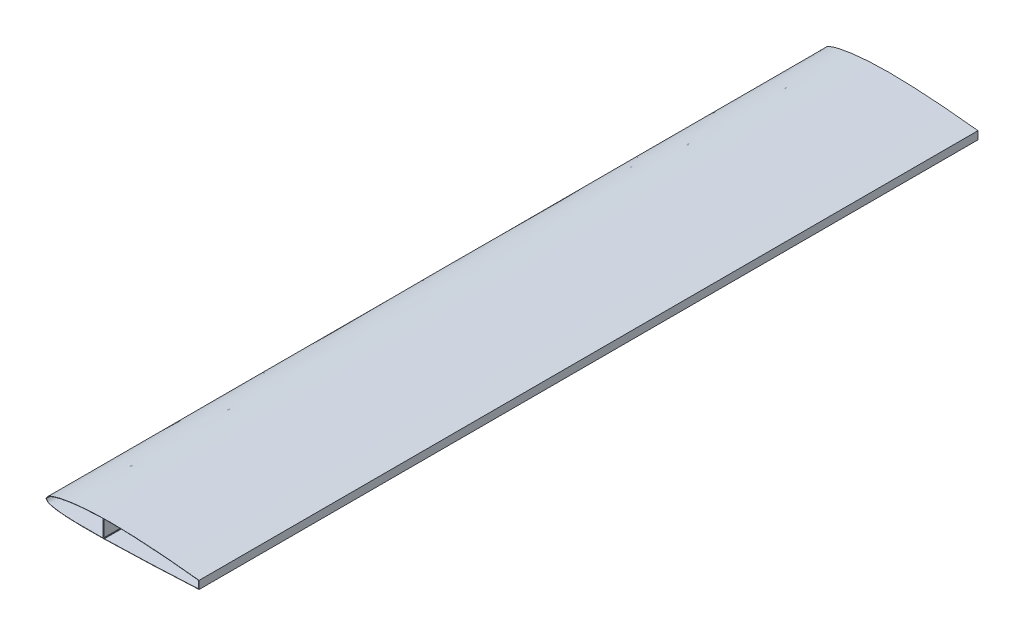
SolidWorks part; units mm, degrees
material "2024-T4"
ref_plane "Front Plane" through (0, 0, 0) normal (0, 0, 1) x (1, 0, 0)
ref_plane "Top Plane" through (0, 0, 0) normal (0, 1, 0) x (1, 0, 0)
ref_plane "Right Plane" through (0, 0, 0) normal (1, 0, 0) x (0, 0, -1)
curve "Top"
  spline degree 3 poles (0, 0, 0) (3.9101, 6.7289, 0) (10.5058, 18.0795, 0) (27.0112, 25.6481, 0) (40.59, 31.5719, 0) (54.3011, 36.3192, 0) (67.915, 40.4922, 0) (81.5319, 44.1857, 0) (95.1379, 47.5159, 0) (108.7414, 50.5421, 0) (122.3424, 53.3102, 0) (135.9422, 55.8531, 0) (149.541, 58.1958, 0) (163.1392, 60.3581, 0) (176.737, 62.3558, 0) (190.3344, 64.202, 0) (203.9316, 65.9075, 0) (217.5286, 67.4816, 0) (231.1254, 68.9321, 0) (244.7221, 70.2661, 0) (258.3187, 71.4894, 0) (271.9153, 72.6074, 0) (285.5117, 73.625, 0) (299.1081, 74.5462, 0) (312.7045, 75.3751, 0) (326.3008, 76.1151, 0) (339.8971, 76.7695, 0) (353.4934, 77.341, 0) (367.0896, 77.8326, 0) (380.6858, 78.2467, 0) (394.282, 78.5855, 0) (407.8782, 78.8514, 0) (421.4743, 79.0463, 0) (435.0705, 79.172, 0) (448.6666, 79.2305, 0) (462.2627, 79.2233, 0) (475.8588, 79.1521, 0) (489.4549, 79.0183, 0) (503.051, 78.8233, 0) (516.6471, 78.5684, 0) (530.2431, 78.2555, 0) (543.839, 77.8832, 0) (557.435, 77.469, 0) (571.031, 77.0139, 0) (584.627, 76.5188, 0) (598.223, 75.9847, 0) (611.819, 75.4126, 0) (625.415, 74.8034, 0) (639.011, 74.1578, 0) (652.607, 73.4767, 0) (666.2029, 72.761, 0) (679.7989, 72.0111, 0) (693.3949, 71.228, 0) (706.9909, 70.4122, 0) (720.5869, 69.5644, 0) (734.1828, 68.6851, 0) (747.7788, 67.7749, 0) (761.3748, 66.8344, 0) (774.9708, 65.864, 0) (788.5667, 64.8643, 0) (802.1627, 63.8356, 0) (815.7587, 62.7784, 0) (829.3546, 61.6931, 0) (842.9506, 60.58, 0) (856.5466, 59.4396, 0) (870.1426, 58.2721, 0) (883.7385, 57.0778, 0) (897.3345, 55.8569, 0) (910.9305, 54.6099, 0) (924.5265, 53.3368, 0) (938.1224, 52.0379, 0) (951.7184, 50.7134, 0) (965.3144, 49.3633, 0) (978.9104, 47.988, 0) (992.5063, 46.5875, 0) (1006.1023, 45.1619, 0) (1019.6983, 43.7112, 0) (1033.2943, 42.2356, 0) (1046.8903, 40.7351, 0) (1060.4862, 39.2096, 0) (1074.0822, 37.6593, 0) (1087.6782, 36.0841, 0) (1101.2742, 34.4839, 0) (1114.8702, 32.8588, 0) (1128.4662, 31.2085, 0) (1142.0622, 29.5331, 0) (1155.6581, 27.8325, 0) (1169.2541, 26.1064, 0) (1182.8501, 24.3548, 0) (1196.4461, 22.5774, 0) (1210.0421, 20.7742, 0) (1223.6381, 18.9448, 0) (1237.2341, 17.0892, 0) (1250.8301, 15.207, 0) (1264.4261, 13.2979, 0) (1278.0221, 11.3619, 0) (1291.6181, 9.3984, 0) (1305.2142, 7.4073, 0) (1318.8101, 5.3878, 0) (1332.4064, 3.3419, 0) (1341.4683, 1.954, 0) (1346, 1.26, 0) knots 0 0 0 0 0.016572 0.027954 0.03876 0.049312 0.059718 0.070028 0.080271 0.090463 0.100615 0.110735 0.12083 0.130902 0.140957 0.150996 0.161021 0.171035 0.181039 0.191035 0.201022 0.211003 0.220979 0.230949 0.240915 0.250877 0.260836 0.270792 0.280746 0.290699 0.300649 0.310598 0.320547 0.330495 0.340442 0.35039 0.360338 0.370286 0.380234 0.390183 0.400133 0.410084 0.420037 0.42999 0.439944 0.449899 0.459855 0.469813 0.479771 0.489731 0.499692 0.509655 0.519619 0.529584 0.539551 0.549519 0.559489 0.56946 0.579433 0.589407 0.599383 0.609361 0.61934 0.629321 0.639303 0.649287 0.659273 0.66926 0.67925 0.689241 0.699233 0.709228 0.719224 0.729223 0.739223 0.749225 0.759229 0.769235 0.779242 0.789252 0.799264 0.809278 0.819294 0.829313 0.839333 0.849356 0.859381 0.869408 0.879438 0.88947 0.899505 0.909542 0.919581 0.929624 0.939669 0.949717 0.959767 0.969821 0.979878 0.989937 1 1 1 1
curve "Bot"
  spline degree 3 poles (0, 0, 0) (3.9391, -6.157, 0) (10.6258, -16.6087, 0) (27.1033, -21.7439, 0) (40.6414, -25.7752, 0) (54.341, -28.6555, 0) (67.9447, -31.0337, 0) (81.556, -32.9828, 0) (95.1576, -34.6222, 0) (108.758, -36.0091, 0) (122.3566, -37.1896, 0) (135.9545, -38.1961, 0) (149.5518, -39.0537, 0) (163.1487, -39.782, 0) (176.7454, -40.3968, 0) (190.3419, -40.9112, 0) (203.9383, -41.3361, 0) (217.5345, -41.6805, 0) (231.1307, -41.9525, 0) (244.7269, -42.1589, 0) (258.323, -42.3057, 0) (271.9191, -42.3982, 0) (285.5151, -42.4413, 0) (299.1111, -42.4392, 0) (312.7072, -42.3956, 0) (326.3032, -42.3143, 0) (339.8991, -42.1982, 0) (353.4951, -42.0505, 0) (367.0911, -41.8737, 0) (380.6871, -41.6705, 0) (394.283, -41.4431, 0) (407.879, -41.1937, 0) (421.4749, -40.9243, 0) (435.0709, -40.6368, 0) (448.6668, -40.3331, 0) (462.2628, -40.0147, 0) (475.8587, -39.6833, 0) (489.4547, -39.3403, 0) (503.0506, -38.9872, 0) (516.6466, -38.6254, 0) (530.2425, -38.2555, 0) (543.8386, -37.8813, 0) (557.4346, -37.4875, 0) (571.0306, -37.0754, 0) (584.6265, -36.6461, 0) (598.2225, -36.2004, 0) (611.8184, -35.7394, 0) (625.4144, -35.264, 0) (639.0103, -34.7749, 0) (652.6063, -34.2729, 0) (666.2022, -33.7589, 0) (679.7982, -33.2336, 0) (693.3941, -32.6976, 0) (706.9901, -32.1516, 0) (720.586, -31.5963, 0) (734.182, -31.0322, 0) (747.7779, -30.4598, 0) (761.3739, -29.8798, 0) (774.9698, -29.2926, 0) (788.5658, -28.6987, 0) (802.1617, -28.0986, 0) (815.7577, -27.4926, 0) (829.3536, -26.8812, 0) (842.9496, -26.2647, 0) (856.5456, -25.6434, 0) (870.1415, -25.0178, 0) (883.7375, -24.3881, 0) (897.3334, -23.7545, 0) (910.9294, -23.1174, 0) (924.5253, -22.4769, 0) (938.1213, -21.8332, 0) (951.7172, -21.1866, 0) (965.3132, -20.5372, 0) (978.9092, -19.8852, 0) (992.5051, -19.2306, 0) (1006.1011, -18.5736, 0) (1019.697, -17.9143, 0) (1033.293, -17.2526, 0) (1046.8889, -16.5888, 0) (1060.4849, -15.9227, 0) (1074.0809, -15.2544, 0) (1087.6768, -14.5838, 0) (1101.2728, -13.911, 0) (1114.8687, -13.2359, 0) (1128.4647, -12.5583, 0) (1142.0607, -11.8783, 0) (1155.6566, -11.1957, 0) (1169.2526, -10.5103, 0) (1182.8486, -9.8221, 0) (1196.4445, -9.1308, 0) (1210.0405, -8.4363, 0) (1223.6365, -7.7383, 0) (1237.2324, -7.0368, 0) (1250.8284, -6.3313, 0) (1264.4244, -5.6217, 0) (1278.0203, -4.9077, 0) (1291.6163, -4.1891, 0) (1305.2123, -3.4654, 0) (1318.8082, -2.7363, 0) (1332.4042, -2.002, 0) (1341.468, -1.5073, 0) (1346, -1.26, 0) knots 0 0 0 0 0.01554 0.02638 0.036798 0.047053 0.057224 0.067347 0.077439 0.08751 0.097567 0.107613 0.117652 0.127685 0.137714 0.14774 0.157763 0.167785 0.177806 0.187826 0.197845 0.207864 0.217882 0.227901 0.23792 0.247939 0.257958 0.267977 0.277996 0.288016 0.298036 0.308056 0.318077 0.328098 0.338119 0.34814 0.358162 0.368184 0.378206 0.388228 0.39825 0.408273 0.418296 0.428319 0.438343 0.448367 0.458391 0.468416 0.478441 0.488466 0.498492 0.508518 0.518545 0.528571 0.538598 0.548626 0.558653 0.568681 0.578709 0.588737 0.598765 0.608794 0.618823 0.628852 0.638881 0.64891 0.658939 0.668969 0.678999 0.689028 0.699058 0.709088 0.719118 0.729148 0.739179 0.749209 0.759239 0.76927 0.7793 0.789331 0.799362 0.809393 0.819424 0.829455 0.839486 0.849517 0.859548 0.869579 0.879611 0.889642 0.899674 0.909706 0.919738 0.92977 0.939802 0.949835 0.959867 0.9699 0.979933 0.989967 1 1 1 1
sketch "Sketch3" plane through (0, 0, 0) normal (0, 0, 1) x (1, 0, 0)
  line L1 (0, 0) -> (1076.8, 0) construction
  line L2 (1076.8, 37.3423) -> (1076.8, -15.1201)
  line L3 (1078.8, 39.1249) -> (1078.8, -17.024)
  line L4 (1077.8, 38.2336) -> (1077.8, -16.072) construction
  spline S0 degree 3 poles (-1345.7363, -1475.2093) (73.9863, 287.8593) (-51.0903, 2.6251) (27.1033, -21.7439) (40.6414, -25.7752) (54.341, -28.6555) (67.9447, -31.0337) (81.556, -32.9828) (95.1576, -34.6222) (108.758, -36.0091) (122.3566, -37.1896) (135.9545, -38.1961) (149.5518, -39.0537) (163.1487, -39.782) (176.7454, -40.3968) (190.3419, -40.9112) (203.9383, -41.3361) (217.5345, -41.6805) (231.1307, -41.9525) (244.7269, -42.1589) (258.323, -42.3057) (271.9191, -42.3982) (285.5151, -42.4413) (299.1111, -42.4392) (312.7072, -42.3956) (326.3032, -42.3143) (339.8991, -42.1982) (353.4951, -42.0505) (367.0911, -41.8737) (380.6871, -41.6705) (394.283, -41.4431) (407.879, -41.1937) (421.4749, -40.9243) (435.0709, -40.6368) (448.6668, -40.3331) (462.2628, -40.0147) (475.8587, -39.6833) (489.4547, -39.3403) (503.0506, -38.9872) (516.6466, -38.6254) (530.2425, -38.2555) (543.8386, -37.8813) (557.4346, -37.4875) (571.0306, -37.0754) (584.6265, -36.6461) (598.2225, -36.2004) (611.8184, -35.7394) (625.4144, -35.264) (639.0103, -34.7749) (652.6063, -34.2729) (666.2022, -33.7589) (679.7982, -33.2336) (693.3941, -32.6976) (706.9901, -32.1516) (720.586, -31.5963) (734.182, -31.0322) (747.7779, -30.4598) (761.3739, -29.8798) (774.9698, -29.2926) (788.5658, -28.6987) (802.1617, -28.0986) (815.7577, -27.4926) (829.3536, -26.8812) (842.9496, -26.2647) (856.5456, -25.6434) (870.1415, -25.0178) (883.7375, -24.3881) (897.3334, -23.7545) (910.9294, -23.1174) (924.5253, -22.4769) (938.1213, -21.8332) (951.7172, -21.1866) (965.3132, -20.5372) (978.9092, -19.8852) (992.5051, -19.2306) (1006.1011, -18.5736) (1019.697, -17.9143) (1033.293, -17.2526) (1046.8889, -16.5888) (1060.4849, -15.9227) (1074.0809, -15.2544) (1087.6768, -14.5838) (1101.2728, -13.911) (1114.8687, -13.2359) (1128.4647, -12.5583) (1142.0607, -11.8783) (1155.6566, -11.1957) (1169.2526, -10.5103) (1182.8486, -9.8221) (1196.4445, -9.1308) (1210.0405, -8.4363) (1223.6365, -7.7383) (1237.2324, -7.0368) (1250.8284, -6.3313) (1264.4244, -5.6217) (1278.0203, -4.9077) (1291.6163, -4.1891) (1305.2123, -3.4654) (1318.8082, -2.7363) (1786.1325, 22.5031) (2248.1969, 60.8937) (2777.2036, -1216.076) knots -0.137826 -0.137826 -0.137826 -0.137826 0.01554 0.02638 0.036798 0.047053 0.057224 0.067347 0.077439 0.08751 0.097567 0.107613 0.117652 0.127685 0.137714 0.14774 0.157763 0.167785 0.177806 0.187826 0.197845 0.207864 0.217882 0.227901 0.23792 0.247939 0.257958 0.267977 0.277996 0.288016 0.298036 0.308056 0.318077 0.328098 0.338119 0.34814 0.358162 0.368184 0.378206 0.388228 0.39825 0.408273 0.418296 0.428319 0.438343 0.448367 0.458391 0.468416 0.478441 0.488466 0.498492 0.508518 0.518545 0.528571 0.538598 0.548626 0.558653 0.568681 0.578709 0.588737 0.598765 0.608794 0.618823 0.628852 0.638881 0.64891 0.658939 0.668969 0.678999 0.689028 0.699058 0.709088 0.719118 0.729148 0.739179 0.749209 0.759239 0.76927 0.7793 0.789331 0.799362 0.809393 0.819424 0.829455 0.839486 0.849517 0.859548 0.869579 0.879611 0.889642 0.899674 0.909706 0.919738 0.92977 0.939802 0.949835 0.959867 0.9699 0.979933 0.989967 2.004497 2.004497 2.004497 2.004497 only from (0, 0) to (1346, -1.26) construction
  spline S1 degree 3 poles (-1478.3902, 1341.2037) (85.3471, -283.5176) (-53.2012, -11.1336) (27.0112, 25.6481) (40.59, 31.5719) (54.3011, 36.3192) (67.915, 40.4922) (81.5319, 44.1857) (95.1379, 47.5159) (108.7414, 50.5421) (122.3424, 53.3102) (135.9422, 55.8531) (149.541, 58.1958) (163.1392, 60.3581) (176.737, 62.3558) (190.3344, 64.202) (203.9316, 65.9075) (217.5286, 67.4816) (231.1254, 68.9321) (244.7221, 70.2661) (258.3187, 71.4894) (271.9153, 72.6074) (285.5117, 73.625) (299.1081, 74.5462) (312.7045, 75.3751) (326.3008, 76.1151) (339.8971, 76.7695) (353.4934, 77.341) (367.0896, 77.8326) (380.6858, 78.2467) (394.282, 78.5855) (407.8782, 78.8514) (421.4743, 79.0463) (435.0705, 79.172) (448.6666, 79.2305) (462.2627, 79.2233) (475.8588, 79.1521) (489.4549, 79.0183) (503.051, 78.8233) (516.6471, 78.5684) (530.2431, 78.2555) (543.839, 77.8832) (557.435, 77.469) (571.031, 77.0139) (584.627, 76.5188) (598.223, 75.9847) (611.819, 75.4126) (625.415, 74.8034) (639.011, 74.1578) (652.607, 73.4767) (666.2029, 72.761) (679.7989, 72.0111) (693.3949, 71.228) (706.9909, 70.4122) (720.5869, 69.5644) (734.1828, 68.6851) (747.7788, 67.7749) (761.3748, 66.8344) (774.9708, 65.864) (788.5667, 64.8643) (802.1627, 63.8356) (815.7587, 62.7784) (829.3546, 61.6931) (842.9506, 60.58) (856.5466, 59.4396) (870.1426, 58.2721) (883.7385, 57.0778) (897.3345, 55.8569) (910.9305, 54.6099) (924.5265, 53.3368) (938.1224, 52.0379) (951.7184, 50.7134) (965.3144, 49.3633) (978.9104, 47.988) (992.5063, 46.5875) (1006.1023, 45.1619) (1019.6983, 43.7112) (1033.2943, 42.2356) (1046.8903, 40.7351) (1060.4862, 39.2096) (1074.0822, 37.6593) (1087.6782, 36.0841) (1101.2742, 34.4839) (1114.8702, 32.8588) (1128.4662, 31.2085) (1142.0622, 29.5331) (1155.6581, 27.8325) (1169.2541, 26.1064) (1182.8501, 24.3548) (1196.4461, 22.5774) (1210.0421, 20.7742) (1223.6381, 18.9448) (1237.2341, 17.0892) (1250.8301, 15.207) (1264.4261, 13.2979) (1278.0221, 11.3619) (1291.6181, 9.3984) (1305.2142, 7.4073) (1318.8101, 5.3878) (1630.3994, -41.4976) (1933.3109, -114.9683) (2496.3588, 1552.4265) knots -0.149606 -0.149606 -0.149606 -0.149606 0.016572 0.027954 0.03876 0.049312 0.059718 0.070028 0.080271 0.090463 0.100615 0.110735 0.12083 0.130902 0.140957 0.150996 0.161021 0.171035 0.181039 0.191035 0.201022 0.211003 0.220979 0.230949 0.240915 0.250877 0.260836 0.270792 0.280746 0.290699 0.300649 0.310598 0.320547 0.330495 0.340442 0.35039 0.360338 0.370286 0.380234 0.390183 0.400133 0.410084 0.420037 0.42999 0.439944 0.449899 0.459855 0.469813 0.479771 0.489731 0.499692 0.509655 0.519619 0.529584 0.539551 0.549519 0.559489 0.56946 0.579433 0.589407 0.599383 0.609361 0.61934 0.629321 0.639303 0.649287 0.659273 0.66926 0.67925 0.689241 0.699233 0.709228 0.719224 0.729223 0.739223 0.749225 0.759229 0.769235 0.779242 0.789252 0.799264 0.809278 0.819294 0.829313 0.839333 0.849356 0.859381 0.869408 0.879438 0.88947 0.899505 0.909542 0.919581 0.929624 0.939669 0.949717 0.959767 0.969821 0.979878 0.989937 1.661442 1.661442 1.661442 1.661442 only from (0, 0) to (1346, 1.26) construction
  spline S2 degree 3 poles (0, 0) (3.9391, -6.157) (10.6258, -16.6087) (27.1033, -21.7439) (40.6414, -25.7752) (54.341, -28.6555) (67.9447, -31.0337) (81.556, -32.9828) (95.1576, -34.6222) (108.758, -36.0091) (122.3566, -37.1896) (135.9545, -38.1961) (149.5518, -39.0537) (163.1487, -39.782) (176.7454, -40.3968) (190.3419, -40.9112) (203.9383, -41.3361) (217.5345, -41.6805) (231.1307, -41.9525) (244.7269, -42.1589) (258.323, -42.3057) (271.9191, -42.3982) (285.5151, -42.4413) (299.1111, -42.4392) (312.7072, -42.3956) (326.3032, -42.3143) (339.8991, -42.1982) (353.4951, -42.0505) (367.0911, -41.8737) (380.6871, -41.6705) (394.283, -41.4431) (407.879, -41.1937) (421.4749, -40.9243) (435.0709, -40.6368) (448.6668, -40.3331) (462.2628, -40.0147) (475.8587, -39.6833) (489.4547, -39.3403) (503.0506, -38.9872) (516.6466, -38.6254) (530.2425, -38.2555) (543.8386, -37.8813) (557.4346, -37.4875) (571.0306, -37.0754) (584.6265, -36.6461) (598.2225, -36.2004) (611.8184, -35.7394) (625.4144, -35.264) (639.0103, -34.7749) (652.6063, -34.2729) (666.2022, -33.7589) (679.7982, -33.2336) (693.3941, -32.6976) (706.9901, -32.1516) (720.586, -31.5963) (734.182, -31.0322) (747.7779, -30.4598) (761.3739, -29.8798) (774.9698, -29.2926) (788.5658, -28.6987) (802.1617, -28.0986) (815.7577, -27.4926) (829.3536, -26.8812) (842.9496, -26.2647) (856.5456, -25.6434) (870.1415, -25.0178) (883.7375, -24.3881) (897.3334, -23.7545) (910.9294, -23.1174) (924.5253, -22.4769) (938.1213, -21.8332) (951.7172, -21.1866) (965.3132, -20.5372) (978.9092, -19.8852) (992.5051, -19.2306) (1006.1011, -18.5736) (1019.697, -17.9143) (1033.293, -17.2526) (1046.8889, -16.5888) (1060.4849, -15.9227) (1070.4552, -15.4326) (1075.8936, -15.1647) (1076.8, -15.1201) knots 0 0 0 0 0.01554 0.02638 0.036798 0.047053 0.057224 0.067347 0.077439 0.08751 0.097567 0.107613 0.117652 0.127685 0.137714 0.14774 0.157763 0.167785 0.177806 0.187826 0.197845 0.207864 0.217882 0.227901 0.23792 0.247939 0.257958 0.267977 0.277996 0.288016 0.298036 0.308056 0.318077 0.328098 0.338119 0.34814 0.358162 0.368184 0.378206 0.388228 0.39825 0.408273 0.418296 0.428319 0.438343 0.448367 0.458391 0.468416 0.478441 0.488466 0.498492 0.508518 0.518545 0.528571 0.538598 0.548626 0.558653 0.568681 0.578709 0.588737 0.598765 0.608794 0.618823 0.628852 0.638881 0.64891 0.658939 0.668969 0.678999 0.689028 0.699058 0.709088 0.719118 0.729148 0.739179 0.749209 0.759239 0.76927 0.7793 0.789331 0.799362 0.801368 0.801368 0.801368 0.801368
  spline S3 degree 3 poles (0, 0) (3.9101, 6.7289) (10.5058, 18.0795) (27.0112, 25.6481) (40.59, 31.5719) (54.3011, 36.3192) (67.915, 40.4922) (81.5319, 44.1857) (95.1379, 47.5159) (108.7414, 50.5421) (122.3424, 53.3102) (135.9422, 55.8531) (149.541, 58.1958) (163.1392, 60.3581) (176.737, 62.3558) (190.3344, 64.202) (203.9316, 65.9075) (217.5286, 67.4816) (231.1254, 68.9321) (244.7221, 70.2661) (258.3187, 71.4894) (271.9153, 72.6074) (285.5117, 73.625) (299.1081, 74.5462) (312.7045, 75.3751) (326.3008, 76.1151) (339.8971, 76.7695) (353.4934, 77.341) (367.0896, 77.8326) (380.6858, 78.2467) (394.282, 78.5855) (407.8782, 78.8514) (421.4743, 79.0463) (435.0705, 79.172) (448.6666, 79.2305) (462.2627, 79.2233) (475.8588, 79.1521) (489.4549, 79.0183) (503.051, 78.8233) (516.6471, 78.5684) (530.2431, 78.2555) (543.839, 77.8832) (557.435, 77.469) (571.031, 77.0139) (584.627, 76.5188) (598.223, 75.9847) (611.819, 75.4126) (625.415, 74.8034) (639.011, 74.1578) (652.607, 73.4767) (666.2029, 72.761) (679.7989, 72.0111) (693.3949, 71.228) (706.9909, 70.4122) (720.5869, 69.5644) (734.1828, 68.6851) (747.7788, 67.7749) (761.3748, 66.8344) (774.9708, 65.864) (788.5667, 64.8643) (802.1627, 63.8356) (815.7587, 62.7784) (829.3546, 61.6931) (842.9506, 60.58) (856.5466, 59.4396) (870.1426, 58.2721) (883.7385, 57.0778) (897.3345, 55.8569) (910.9305, 54.6099) (924.5265, 53.3368) (938.1224, 52.0379) (951.7184, 50.7134) (965.3144, 49.3633) (978.9104, 47.988) (992.5063, 46.5875) (1006.1023, 45.1619) (1019.6983, 43.7112) (1033.2943, 42.2356) (1046.8903, 40.7351) (1060.4862, 39.2096) (1070.4558, 38.0728) (1075.8936, 37.4468) (1076.8, 37.3423) knots 0 0 0 0 0.016572 0.027954 0.03876 0.049312 0.059718 0.070028 0.080271 0.090463 0.100615 0.110735 0.12083 0.130902 0.140957 0.150996 0.161021 0.171035 0.181039 0.191035 0.201022 0.211003 0.220979 0.230949 0.240915 0.250877 0.260836 0.270792 0.280746 0.290699 0.300649 0.310598 0.320547 0.330495 0.340442 0.35039 0.360338 0.370286 0.380234 0.390183 0.400133 0.410084 0.420037 0.42999 0.439944 0.449899 0.459855 0.469813 0.479771 0.489731 0.499692 0.509655 0.519619 0.529584 0.539551 0.549519 0.559489 0.56946 0.579433 0.589407 0.599383 0.609361 0.61934 0.629321 0.639303 0.649287 0.659273 0.66926 0.67925 0.689241 0.699233 0.709228 0.719224 0.729223 0.739223 0.749225 0.759229 0.769235 0.779242 0.789252 0.799264 0.801267 0.801267 0.801267 0.801267
  spline S4 degree 1 poles (-2.3423, -0.0501) (1078.8, 39.1249) knots 0 0 1 1 construction
  spline S5 degree 1 poles (-2.3423, -0.0501) (1078.8, -17.024) knots 0 0 1 1 construction
  spline S6 degree 3 poles (-2.3423, -0.0501) (-1.6, 1.2273) (-0.1239, 3.779) (2.9437, 8.8794) (6.3349, 13.7678) (10.3862, 18.1012) (15.0404, 21.9084) (20.3074, 24.7496) (25.6582, 27.189) (30.9269, 29.5304) (37.5188, 32.3647) (45.6119, 35.4376) (53.8075, 38.2034) (62.0293, 40.7876) (73.0602, 44.0048) (86.9482, 47.6379) (103.7129, 51.5271) (120.5574, 55.0189) (137.4615, 58.1736) (160.0647, 61.9848) (188.415, 66.0912) (222.5404, 70.1483) (268.1403, 74.5554) (325.2702, 78.4122) (393.9239, 80.8747) (462.6085, 81.485) (519.8399, 80.6267) (565.595, 79.235) (611.3375, 77.5245) (668.4885, 74.7772) (737.0202, 70.6273) (828.3242, 64.0562) (942.3128, 54.07) (1033.3349, 44.3675) (1078.8, 39.1249) knots -0.000866 -0.000866 -0.000866 -0.000866 0.002272 0.005411 0.011688 0.014826 0.017965 0.024241 0.02738 0.030518 0.036795 0.043072 0.049349 0.055626 0.061903 0.074456 0.08701 0.099564 0.112117 0.124671 0.149778 0.174886 0.199993 0.250208 0.300423 0.350638 0.400853 0.42596 0.451067 0.501282 0.551497 0.601712 0.702142 0.802571 0.802571 0.802571 0.802571
  spline S7 degree 3 poles (1078.8, -17.024) (1033.4128, -19.2602) (942.6355, -23.6666) (829.1506, -28.9455) (738.3475, -32.8923) (670.2344, -35.6476) (602.1093, -38.141) (533.963, -40.2016) (465.8213, -41.9736) (397.6627, -43.4705) (329.4876, -44.4237) (272.659, -44.522) (227.1917, -43.9403) (193.0929, -43.0814) (164.6845, -41.9119) (141.9695, -40.6098) (124.9427, -39.4152) (107.9295, -37.9597) (90.94, -36.1793) (73.9782, -33.9994) (59.9073, -31.7048) (48.6822, -29.5247) (40.279, -27.6227) (33.4193, -25.7053) (27.9441, -24.059) (22.3993, -22.3798) (16.7474, -20.3948) (11.5704, -17.3067) (8.1835, -14.3926) (5.2058, -11.0896) (2.5272, -7.5161) (0.0413, -3.7895) (-1.5442, -1.2975) (-2.3423, -0.0501) knots -0.000865 -0.000865 -0.000865 -0.000865 0.09959 0.200044 0.250271 0.300499 0.350726 0.400953 0.45118 0.501408 0.551635 0.601862 0.626976 0.652089 0.677203 0.68976 0.702316 0.714873 0.72743 0.739987 0.752544 0.758822 0.7651 0.771379 0.774518 0.777657 0.783936 0.787075 0.790214 0.793353 0.796493 0.799632 0.802771 0.802771 0.802771 0.802771
  spline S8 degree 1 poles (-1.1711, -0.025) (1077.8, 38.2336) knots 0 0 1 1 construction
  spline S9 degree 1 poles (-1.1711, -0.025) (1077.8, -16.072) knots 0 0 1 1 construction
  spline S10 degree 3 poles (-1.1711, -0.025) (0.3089, 2.522) (3.264, 7.6454) (7.486, 13.6061) (11.4944, 17.7626) (16.0623, 21.3572) (21.2534, 24.0957) (26.5637, 26.4967) (31.8182, 28.8303) (38.3804, 31.6349) (46.4306, 34.6654) (57.3121, 38.321) (71.0086, 42.4438) (87.6283, 46.7743) (104.3469, 50.6419) (121.1496, 54.1158) (138.0139, 57.2557) (160.5662, 61.0501) (188.8564, 65.14) (222.9131, 69.1821) (268.4248, 73.5741) (325.4493, 77.4189) (393.9812, 79.8748) (462.5484, 80.4843) (519.6822, 79.6298) (565.3652, 78.2421) (611.0363, 76.5364) (668.0993, 73.7965) (736.5269, 69.6574) (827.6937, 63.1034) (941.5127, 53.1394) (1032.4023, 43.4684) (1077.8, 38.2336) knots -0.000433 -0.000433 -0.000433 -0.000433 0.005835 0.012104 0.015238 0.018372 0.02464 0.027775 0.030909 0.037177 0.043446 0.049714 0.062251 0.074787 0.087324 0.099861 0.112398 0.124934 0.150008 0.175082 0.200155 0.250302 0.300449 0.350596 0.400743 0.425817 0.45089 0.501037 0.551184 0.601331 0.701625 0.801919 0.801919 0.801919 0.801919 construction
  spline S11 degree 3 poles (1077.8, -16.072) (1032.4774, -18.3051) (941.829, -22.7036) (828.5065, -27.9735) (737.8347, -31.9129) (669.8211, -34.6627) (601.7964, -37.1509) (533.754, -39.2066) (465.7099, -40.9759) (397.654, -42.4702) (329.5847, -43.4224) (272.849, -43.5223) (227.4604, -42.9448) (193.4236, -42.0913) (165.0703, -40.9289) (142.4027, -39.6351) (125.4134, -38.4484) (108.4406, -37.0032) (91.4953, -35.2366) (74.5828, -33.0749) (60.5617, -30.8048) (49.3791, -28.6463) (41.0251, -26.7785) (34.2031, -24.8917) (28.7479, -23.2577) (23.2318, -21.5913) (17.665, -19.6851) (12.6251, -16.822) (9.2974, -14.0774) (6.3537, -10.9083) (2.8023, -6.2684) (0.4183, -2.5094) (-1.1711, -0.025) knots -0.000432 -0.000432 -0.000432 -0.000432 0.09988 0.200193 0.250349 0.300506 0.350662 0.400819 0.450975 0.501131 0.551288 0.601444 0.626522 0.6516 0.676679 0.689218 0.701757 0.714296 0.726835 0.739374 0.751913 0.758183 0.764452 0.770722 0.773856 0.776991 0.783261 0.786396 0.78953 0.792665 0.7958 0.802069 0.802069 0.802069 0.802069 construction
  dimension "D1" = 1076.8
  dimension "D2" = 2
  dimension "D3" = 1
extrude "Skin" add sketch "Sketch3" along normal blind 5500
sketch "Sketch4" plane through (0, 0, 0) normal (0, 0, 1) x (1, 0, 0)
  line L0 (405.8, 79.7676) -> (405.8, -42.2672)
  line L1 (401.8, 79.7676) -> (401.8, -42.2672)
  line L2 (1074.8, 37.5726) -> (1074.8, -15.2186)
  line L3 (1078.8, 37.5726) -> (1078.8, -15.2186)
  line L4 (1074.8, 37.5726) -> (1078.8, 37.5726)
  line L5 (1074.8, -15.2186) -> (1078.8, -15.2186)
  line L6 (405.8, 79.7676) -> (401.8, 79.7676)
  line L7 (405.8, -42.2672) -> (401.8, -42.2672)
  line L8 (403.8, 79.7676) -> (403.8, -42.2672) construction
  line L9 (1076.8, 37.5726) -> (1076.8, -15.2186) construction
  line L10 (1076.8, -15.1201) -> (1076.8, 37.3423) construction
  spline S0 degree 3 poles (1076.8, 37.3423) (1075.8936, 37.4468) (1070.4558, 38.0728) (1060.4862, 39.2096) (1046.8903, 40.7351) (1033.2943, 42.2356) (1019.6983, 43.7112) (1006.1023, 45.1619) (992.5063, 46.5875) (978.9104, 47.988) (965.3144, 49.3633) (951.7184, 50.7134) (938.1224, 52.0379) (924.5265, 53.3368) (910.9305, 54.6099) (897.3345, 55.8569) (883.7385, 57.0778) (870.1426, 58.2721) (856.5466, 59.4396) (842.9506, 60.58) (829.3546, 61.6931) (815.7587, 62.7784) (802.1627, 63.8356) (788.5667, 64.8643) (774.9708, 65.864) (761.3748, 66.8344) (747.7788, 67.7749) (734.1828, 68.6851) (720.5869, 69.5644) (706.9909, 70.4122) (693.3949, 71.228) (679.7989, 72.0111) (666.2029, 72.761) (652.607, 73.4767) (639.011, 74.1578) (625.415, 74.8034) (611.819, 75.4126) (598.223, 75.9847) (584.627, 76.5188) (571.031, 77.0139) (557.435, 77.469) (543.839, 77.8832) (530.2431, 78.2555) (516.6471, 78.5684) (503.051, 78.8233) (489.4549, 79.0183) (475.8588, 79.1521) (462.2627, 79.2233) (448.6666, 79.2305) (435.0705, 79.172) (421.4743, 79.0463) (407.8782, 78.8514) (394.282, 78.5855) (380.6858, 78.2467) (367.0896, 77.8326) (353.4934, 77.341) (339.8971, 76.7695) (326.3008, 76.1151) (312.7045, 75.3751) (299.1081, 74.5462) (285.5117, 73.625) (271.9153, 72.6074) (258.3187, 71.4894) (244.7221, 70.2661) (231.1254, 68.9321) (217.5286, 67.4816) (203.9316, 65.9075) (190.3344, 64.202) (176.737, 62.3558) (163.1392, 60.3581) (149.541, 58.1958) (135.9422, 55.8531) (122.3424, 53.3102) (108.7414, 50.5421) (95.1379, 47.5159) (81.5319, 44.1857) (67.915, 40.4922) (54.3011, 36.3192) (40.59, 31.5719) (27.0112, 25.6481) (10.5058, 18.0795) (3.9101, 6.7289) (0, 0) knots 0.198733 0.198733 0.198733 0.198733 0.200736 0.210748 0.220758 0.230765 0.240771 0.250775 0.260777 0.270777 0.280776 0.290772 0.300767 0.310759 0.32075 0.33074 0.340727 0.350713 0.360697 0.370679 0.38066 0.390639 0.400617 0.410593 0.420567 0.43054 0.440511 0.450481 0.460449 0.470416 0.480381 0.490345 0.500308 0.510269 0.520229 0.530187 0.540145 0.550101 0.560056 0.57001 0.579963 0.589916 0.599867 0.609817 0.619766 0.629714 0.639662 0.64961 0.659558 0.669505 0.679453 0.689402 0.699351 0.709301 0.719254 0.729208 0.739164 0.749123 0.759085 0.769051 0.779021 0.788997 0.798978 0.808965 0.818961 0.828965 0.838979 0.849004 0.859043 0.869098 0.87917 0.889265 0.899385 0.909537 0.919729 0.929972 0.940282 0.950688 0.96124 0.972046 0.983428 1 1 1 1 construction
  spline S1 degree 3 poles (0, 0) (3.9391, -6.157) (10.6258, -16.6087) (27.1033, -21.7439) (40.6414, -25.7752) (54.341, -28.6555) (67.9447, -31.0337) (81.556, -32.9828) (95.1576, -34.6222) (108.758, -36.0091) (122.3566, -37.1896) (135.9545, -38.1961) (149.5518, -39.0537) (163.1487, -39.782) (176.7454, -40.3968) (190.3419, -40.9112) (203.9383, -41.3361) (217.5345, -41.6805) (231.1307, -41.9525) (244.7269, -42.1589) (258.323, -42.3057) (271.9191, -42.3982) (285.5151, -42.4413) (299.1111, -42.4392) (312.7072, -42.3956) (326.3032, -42.3143) (339.8991, -42.1982) (353.4951, -42.0505) (367.0911, -41.8737) (380.6871, -41.6705) (394.283, -41.4431) (407.879, -41.1937) (421.4749, -40.9243) (435.0709, -40.6368) (448.6668, -40.3331) (462.2628, -40.0147) (475.8587, -39.6833) (489.4547, -39.3403) (503.0506, -38.9872) (516.6466, -38.6254) (530.2425, -38.2555) (543.8386, -37.8813) (557.4346, -37.4875) (571.0306, -37.0754) (584.6265, -36.6461) (598.2225, -36.2004) (611.8184, -35.7394) (625.4144, -35.264) (639.0103, -34.7749) (652.6063, -34.2729) (666.2022, -33.7589) (679.7982, -33.2336) (693.3941, -32.6976) (706.9901, -32.1516) (720.586, -31.5963) (734.182, -31.0322) (747.7779, -30.4598) (761.3739, -29.8798) (774.9698, -29.2926) (788.5658, -28.6987) (802.1617, -28.0986) (815.7577, -27.4926) (829.3536, -26.8812) (842.9496, -26.2647) (856.5456, -25.6434) (870.1415, -25.0178) (883.7375, -24.3881) (897.3334, -23.7545) (910.9294, -23.1174) (924.5253, -22.4769) (938.1213, -21.8332) (951.7172, -21.1866) (965.3132, -20.5372) (978.9092, -19.8852) (992.5051, -19.2306) (1006.1011, -18.5736) (1019.697, -17.9143) (1033.293, -17.2526) (1046.8889, -16.5888) (1060.4849, -15.9227) (1070.4552, -15.4326) (1075.8936, -15.1647) (1076.8, -15.1201) knots 0 0 0 0 0.01554 0.02638 0.036798 0.047053 0.057224 0.067347 0.077439 0.08751 0.097567 0.107613 0.117652 0.127685 0.137714 0.14774 0.157763 0.167785 0.177806 0.187826 0.197845 0.207864 0.217882 0.227901 0.23792 0.247939 0.257958 0.267977 0.277996 0.288016 0.298036 0.308056 0.318077 0.328098 0.338119 0.34814 0.358162 0.368184 0.378206 0.388228 0.39825 0.408273 0.418296 0.428319 0.438343 0.448367 0.458391 0.468416 0.478441 0.488466 0.498492 0.508518 0.518545 0.528571 0.538598 0.548626 0.558653 0.568681 0.578709 0.588737 0.598765 0.608794 0.618823 0.628852 0.638881 0.64891 0.658939 0.668969 0.678999 0.689028 0.699058 0.709088 0.719118 0.729148 0.739179 0.749209 0.759239 0.76927 0.7793 0.789331 0.799362 0.801368 0.801368 0.801368 0.801368 construction
  spline S2 degree 3 poles (-1.1711, -0.025) (0.3089, 2.522) (3.264, 7.6454) (7.486, 13.6061) (11.4944, 17.7626) (16.0623, 21.3572) (21.2534, 24.0957) (26.5637, 26.4967) (31.8182, 28.8303) (38.3804, 31.6349) (46.4306, 34.6654) (57.3121, 38.321) (71.0086, 42.4438) (87.6283, 46.7743) (104.3469, 50.6419) (121.1496, 54.1158) (138.0139, 57.2557) (160.5662, 61.0501) (188.8564, 65.14) (222.9131, 69.1821) (268.4248, 73.5741) (325.4493, 77.4189) (393.9812, 79.8748) (462.5484, 80.4843) (519.6822, 79.6298) (565.3652, 78.2421) (611.0363, 76.5364) (668.0993, 73.7965) (736.5269, 69.6574) (827.6937, 63.1034) (941.5127, 53.1394) (1032.4023, 43.4684) (1077.8, 38.2336) knots -0.000433 -0.000433 -0.000433 -0.000433 0.005835 0.012104 0.015238 0.018372 0.02464 0.027775 0.030909 0.037177 0.043446 0.049714 0.062251 0.074787 0.087324 0.099861 0.112398 0.124934 0.150008 0.175082 0.200155 0.250302 0.300449 0.350596 0.400743 0.425817 0.45089 0.501037 0.551184 0.601331 0.701625 0.801919 0.801919 0.801919 0.801919 construction
  spline S3 degree 3 poles (1077.8, -16.072) (1032.4774, -18.3051) (941.829, -22.7036) (828.5065, -27.9735) (737.8347, -31.9129) (669.8211, -34.6627) (601.7964, -37.1509) (533.754, -39.2066) (465.7099, -40.9759) (397.654, -42.4702) (329.5847, -43.4224) (272.849, -43.5223) (227.4604, -42.9448) (193.4236, -42.0913) (165.0703, -40.9289) (142.4027, -39.6351) (125.4134, -38.4484) (108.4406, -37.0032) (91.4953, -35.2366) (74.5828, -33.0749) (60.5617, -30.8048) (49.3791, -28.6463) (41.0251, -26.7785) (34.2031, -24.8917) (28.7479, -23.2577) (23.2318, -21.5913) (17.665, -19.6851) (12.6251, -16.822) (9.2974, -14.0774) (6.3537, -10.9083) (2.8023, -6.2684) (0.4183, -2.5094) (-1.1711, -0.025) knots -0.000432 -0.000432 -0.000432 -0.000432 0.09988 0.200193 0.250349 0.300506 0.350662 0.400819 0.450975 0.501131 0.551288 0.601444 0.626522 0.6516 0.676679 0.689218 0.701757 0.714296 0.726835 0.739374 0.751913 0.758183 0.764452 0.770722 0.773856 0.776991 0.783261 0.786396 0.78953 0.792665 0.7958 0.802069 0.802069 0.802069 0.802069 construction
  dimension "D1" = 4
  dimension "D2" = 403.8
  dimension "D3" = 4
extrude "Spar" add sketch "Sketch4" along normal blind 5500
sketch "Sketch5" plane through (0, 0, 0) normal (0, 0, 1) x (1, 0, 0)
  line L0 (401.8, 74.7298) -> (399.8, 74.7298)
  line L1 (401.8, 78.7295) -> (401.8, -41.3043) construction
  line L2 (399.8, 74.7298) -> (399.8, 76.6495)
  line L3 (399.8, 76.6495) -> (397.8, 76.6495)
  line L4 (397.8, 76.6495) -> (397.8, 79.6495)
  line L5 (397.8, 79.6495) -> (401.8, 79.7298)
  line L6 (401.8, 79.7298) -> (401.8, 74.7298)
  line L7 (405.8, 79.8039) -> (405.8, 74.8039)
  line L8 (405.8, -41.2298) -> (405.8, 78.8035) construction
  line L9 (405.8, 74.8039) -> (407.8002, 74.8039)
  line L10 (407.8002, 74.8039) -> (407.8002, 76.7236)
  line L11 (407.8002, 76.7236) -> (409.8002, 76.7236)
  line L12 (409.8002, 76.7236) -> (409.8002, 79.8719)
  line L13 (409.8002, 79.8719) -> (405.8, 79.8039)
  line L14 (405.8, 79.7676) -> (405.8, -42.2672) construction
  line L15 (401.8, 79.7676) -> (401.8, -42.2672) construction
  line L16 (401.8, -42.3043) -> (397.8, -42.3772)
  line L17 (397.8, -42.3772) -> (397.8, -39.3772)
  line L18 (397.8, -39.3772) -> (399.8, -39.3772)
  line L19 (399.8, -39.3772) -> (399.8, -37.3043)
  line L20 (399.8, -37.3043) -> (401.8, -37.3043)
  line L21 (401.8, -37.3043) -> (401.8, -42.3043)
  line L22 (405.8, -42.2296) -> (405.8, -37.2296)
  line L23 (405.8, -37.2296) -> (407.8, -37.2296)
  line L24 (407.8, -37.2296) -> (407.8, -39.1531)
  line L25 (407.8, -39.1531) -> (409.7999, -39.1531)
  line L26 (409.7999, -39.1531) -> (409.7999, -42.1531)
  line L27 (409.7999, -42.1531) -> (405.8, -42.2296)
  line L28 (1074.8, 38.5789) -> (1070.8, 39.0376)
  line L29 (1074.8, 37.5726) -> (1074.8, -15.2186) construction
  line L30 (1070.8, 39.0376) -> (1070.8, 36.0376)
  line L31 (1070.8, 36.0376) -> (1072.8, 36.0376)
  line L32 (1072.8, 36.0376) -> (1072.8, 33.5789)
  line L33 (1072.8, 33.5789) -> (1074.8, 33.5789)
  line L34 (1074.8, 33.5789) -> (1074.8, 38.5789)
  line L35 (1074.8, -16.2198) -> (1070.7787, -16.4177)
  line L36 (1070.7787, -16.4177) -> (1070.7787, -13.4177)
  line L37 (1070.7787, -13.4177) -> (1072.8, -13.4177)
  line L38 (1072.8, -13.4177) -> (1072.8, -11.2198)
  line L39 (1072.8, -11.2198) -> (1074.8, -11.2198)
  line L40 (1074.8, -11.2198) -> (1074.8, -16.2198)
  spline S4 degree 3 poles (-1.1711, -0.025) (0.3089, 2.522) (3.264, 7.6454) (7.486, 13.6061) (11.4944, 17.7626) (16.0623, 21.3572) (21.2534, 24.0957) (26.5637, 26.4967) (31.8182, 28.8303) (38.3804, 31.6349) (46.4306, 34.6654) (57.3121, 38.321) (71.0086, 42.4438) (87.6283, 46.7743) (104.3469, 50.6419) (121.1496, 54.1158) (138.0139, 57.2557) (160.5662, 61.0501) (188.8564, 65.14) (222.9131, 69.1821) (268.4248, 73.5741) (325.4493, 77.4189) (393.9812, 79.8748) (462.5484, 80.4843) (519.6822, 79.6298) (565.3652, 78.2421) (611.0363, 76.5364) (668.0993, 73.7965) (736.5269, 69.6574) (827.6937, 63.1034) (941.5127, 53.1394) (1032.4023, 43.4684) (1077.8, 38.2336) knots -0.000433 -0.000433 -0.000433 -0.000433 0.005835 0.012104 0.015238 0.018372 0.02464 0.027775 0.030909 0.037177 0.043446 0.049714 0.062251 0.074787 0.087324 0.099861 0.112398 0.124934 0.150008 0.175082 0.200155 0.250302 0.300449 0.350596 0.400743 0.425817 0.45089 0.501037 0.551184 0.601331 0.701625 0.801919 0.801919 0.801919 0.801919 construction
  spline S5 degree 3 poles (1077.8, -16.072) (1032.4774, -18.3051) (941.829, -22.7036) (828.5065, -27.9735) (737.8347, -31.9129) (669.8211, -34.6627) (601.7964, -37.1509) (533.754, -39.2066) (465.7099, -40.9759) (397.654, -42.4702) (329.5847, -43.4224) (272.849, -43.5223) (227.4604, -42.9448) (193.4236, -42.0913) (165.0703, -40.9289) (142.4027, -39.6351) (125.4134, -38.4484) (108.4406, -37.0032) (91.4953, -35.2366) (74.5828, -33.0749) (60.5617, -30.8048) (49.3791, -28.6463) (41.0251, -26.7785) (34.2031, -24.8917) (28.7479, -23.2577) (23.2318, -21.5913) (17.665, -19.6851) (12.6251, -16.822) (9.2974, -14.0774) (6.3537, -10.9083) (2.8023, -6.2684) (0.4183, -2.5094) (-1.1711, -0.025) knots -0.000432 -0.000432 -0.000432 -0.000432 0.09988 0.200193 0.250349 0.300506 0.350662 0.400819 0.450975 0.501131 0.551288 0.601444 0.626522 0.6516 0.676679 0.689218 0.701757 0.714296 0.726835 0.739374 0.751913 0.758183 0.764452 0.770722 0.773856 0.776991 0.783261 0.786396 0.78953 0.792665 0.7958 0.802069 0.802069 0.802069 0.802069 construction
  dimension "D1" = 2
  dimension "D2" = 3
  dimension "D3" = 5
  dimension "D4" = 4
  dimension "D5" = 5
  dimension "D6" = 3
  dimension "D7" = 5
  dimension "D8" = 2
  dimension "D9" = 4
  dimension "D10" = 2
  dimension "D11" = 4
  dimension "D12" = 3
extrude "Boss-Extrude7" add sketch "Sketch5" along normal blind 5500
